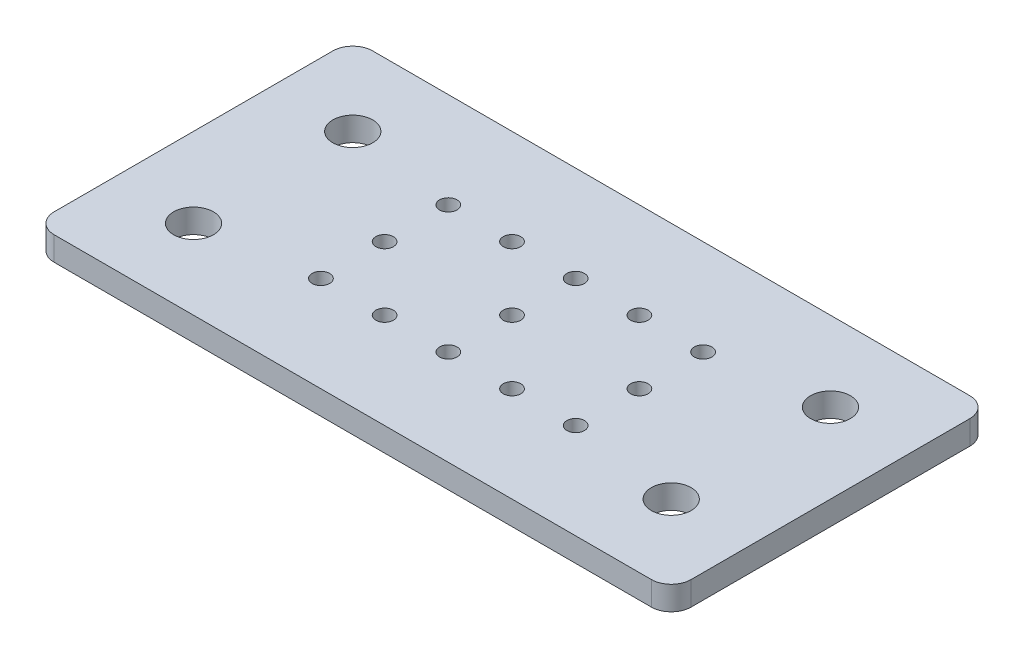
SolidWorks part; units mm, degrees
ref_plane "Face" through (0, 0, 0) normal (0, 0, 1) x (1, 0, 0)
ref_plane "Dessus" through (0, 0, 0) normal (0, 1, 0) x (1, 0, 0)
ref_plane "Droite" through (0, 0, 0) normal (1, 0, 0) x (0, 0, -1)
sketch "Esquisse1" plane through (0, 0, 0) normal (0, 1, 0) x (1, 0, 0)
  line L0 (0, 10) -> (80, 10) construction
  line L1 (0, 0) -> (80, 0)
  line L2 (0, 0) -> (0, 40)
  line L3 (0, 40) -> (80, 40)
  line L4 (80, 0) -> (80, 40)
  line L5 (40, 40) -> (40, 0) construction
  line L6 (0, 20) -> (80, 20) construction
  line L7 (56, 0) -> (56, 28) construction
  line L9 (48, 28) -> (48, 0) construction
  line L10 (48, 28) -> (56, 28) construction
  line L11 (48, 20) -> (56, 20) construction
  line L12 (48, 12) -> (56, 12) construction
  line L13 (40, 0) -> (40, 28) construction
  line L15 (48, 28) -> (40, 28) construction
  line L16 (48, 20) -> (40, 20) construction
  line L17 (48, 12) -> (40, 12) construction
  circle A0 centre (10, 10) radius 2.5
  circle A1 centre (70, 10) radius 2.5
  circle A2 centre (70, 30) radius 2.5
  circle A3 centre (10, 30) radius 2.5
  circle A4 centre (40, 28) radius 1.1
  circle A5 centre (48, 28) radius 1.1
  circle A6 centre (56, 28) radius 1.1
  circle A7 centre (40, 20) radius 1.1
  circle A8 centre (24, 12) radius 1.1
  circle A9 centre (56, 20) radius 1.1
  circle A10 centre (40, 12) radius 1.1
  circle A11 centre (48, 12) radius 1.1
  circle A12 centre (56, 12) radius 1.1
  circle A13 centre (32, 12) radius 1.1
  circle A14 centre (24, 20) radius 1.1
  circle A15 centre (24, 28) radius 1.1
  circle A16 centre (32, 28) radius 1.1
  dimension "D3" = 5
  dimension "D12" = 2.2
  dimension "D1" = 40
  dimension "D2" = 80
  dimension "D4" = 10
  dimension "D5" = 10
  dimension "D7" = 8
  dimension "D9" = 8
  dimension "D10" = 8
  dimension "D11" = 8
extrude "Extrusion1" add sketch "Esquisse1" along normal blind 3
fillet "Congé1" radius 2.5 4 edges at (0, 1.5, -40) (80, 1.5, -40) (80, 1.5, 0) (0, 1.5, 0)
